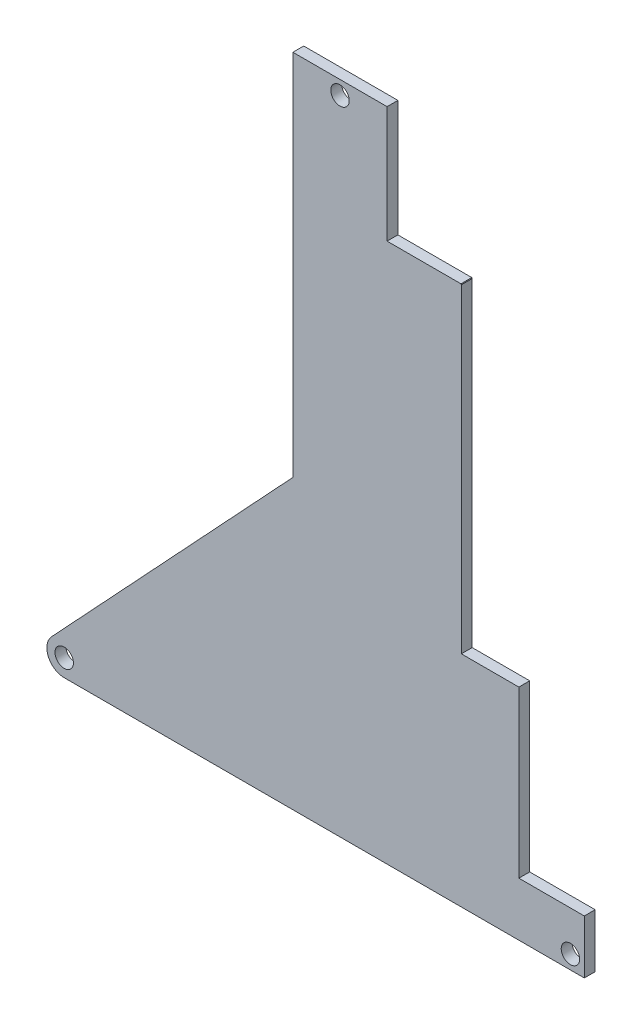
SolidWorks part; units mm, degrees
ref_plane "Front Plane" through (0, 0, 0) normal (0, 0, 1) x (1, 0, 0)
ref_plane "Top Plane" through (0, 0, 0) normal (0, 1, 0) x (1, 0, 0)
ref_plane "Right Plane" through (0, 0, 0) normal (1, 0, 0) x (0, 0, -1)
sketch "Sketch1" plane through (0, 0, 0) normal (0, 0, 1) x (1, 0, 0)
  line L1 (-52.6486, -67.2724) -> (-30.5784, -43.6209)
  line L3 (-30.5784, -43.6209) -> (-18.8373, -31.0385)
  line L4 (-18.8373, 22.9178) -> (-18.8373, 15.0967)
  line L5 (-62.4049, -73.074) -> (-22.4391, -30.2446) construction
  line L6 (-54.2124, -68.9483) -> (-52.6486, -67.2724)
  line L7 (-60.0836, -75.2401) -> (-20.1178, -32.4107) construction
  line L9 (23.8665, -73.2212) -> (-30.5784, -73.2212)
  line L12 (-18.8373, 15.0967) -> (-18.8373, -31.0385)
  line L13 (-30.5784, -73.2212) -> (-52.3554, -73.2212)
  line L14 (-18.8373, 22.9178) -> (-5.0365, 22.9178)
  line L20 (23.8665, -65.3472) -> (23.8665, -73.2212)
  arc A1 (25.454, -65.3472) -> (-3.6178, 23.6674) centre (-125.3585, -65.3472) ccw construction
  arc A2 (23.8665, -65.3472) -> (-5.0365, 22.9178) centre (-125.3585, -65.3472) ccw
  arc A3 (23.8665, -65.3472) -> (-4.8993, 22.7304) centre (-125.3585, -65.3472) ccw construction
  arc A7 (-52.3554, -73.2212) -> (-54.2124, -68.9483) centre (-52.3554, -70.6812) cw
  dimension "D5" = 2.54
  dimension "D1" = 1.5875
  dimension "D2" = 3.175
extrude "Boss-Extrude1" add sketch "Sketch1" along normal blind 1.5875
hole_wizard "#2 Clearance Hole1" positions "Sketch3" profile "Sketch2" hole size "#2" standard "ANSI Inch" end condition through all
sketch "Sketch3" plane through (0, 0, 0) normal (0, 0, -1) x (-1, 0, 0)
  line L0 (11.9369, 20.8858) -> (11.9369, 22.9178) construction
  line L1 (5.0365, 22.9178) -> (18.8373, 22.9178) construction
  line L2 (-23.8665, -73.2212) -> (-23.8665, -65.3472) construction
  line L3 (52.3554, -73.2212) -> (-23.8665, -73.2212) construction
  point P0 (-21.8345, -71.1892)
  point P2 (52.3554, -70.6812)
  point P5 (11.9369, 20.8858)
  dimension "D1" = 2.032
  dimension "D2" = 2.032
  dimension "D3" = 2.032
sketch "Sketch2" plane through (21.8345, -71.1892, 0) normal (1, 0, 0) x (0, 1, 0)
  line L0 (0, 0) -> (0, 1.5875)
  line L1 (0, 1.5875) -> (1.3525, 1.5875)
  line L2 (1.3525, 1.5875) -> (1.3525, 0)
  line L5 (1.3525, 0) -> (0, 0)
  line L11 (0, -6.35) -> (0, 107.95) construction
  dimension "Thru Hole Dia." = 2.7051
  dimension "Thru Hole Depth" = 1.5875
sketch "Sketch4" plane through (0, 0, 0) normal (0, 0, -1) x (-1, 0, 0)
  line L1 (-23.8665, -65.3472) -> (-14.278, -65.3472)
  line L2 (-23.8665, -65.3472) -> (-23.8665, -41.0902)
  line L3 (-23.8665, -41.0902) -> (-14.278, -41.0902)
  line L4 (-14.278, -65.3472) -> (-14.278, -41.0902)
  line L5 (-23.8665, -65.3472) -> (-14.278, -41.0902) construction
  line L6 (-23.8665, -41.0902) -> (-14.278, -65.3472) construction
  line L8 (-14.278, -41.0902) -> (-9.1472, -41.0902) construction
  line L9 (-14.278, -73.9832) -> (-14.278, -41.0902) construction
  line L10 (-5.8452, 5.8452) -> (-21.8817, 5.8452)
  line L11 (-5.8452, 5.8452) -> (-5.8452, -41.0902)
  line L12 (-5.8452, -41.0902) -> (-21.8817, -41.0902)
  line L13 (-21.8817, 5.8452) -> (-21.8817, -41.0902)
  line L14 (-5.8452, 5.8452) -> (-21.8817, -41.0902) construction
  line L15 (-5.8452, -41.0902) -> (-21.8817, 5.8452) construction
  line L16 (5.0365, 22.9178) -> (-5.8452, 22.9178)
  line L17 (5.0365, 22.9178) -> (5.0365, 5.8452)
  line L18 (5.0365, 5.8452) -> (-5.8452, 5.8452)
  line L19 (-5.8452, 22.9178) -> (-5.8452, 5.8452)
  line L20 (5.0365, 22.9178) -> (-5.8452, 5.8452) construction
  line L21 (5.0365, 5.8452) -> (-5.8452, 22.9178) construction
  arc A0 (5.0365, 22.9178) -> (-23.8665, -65.3472) centre (125.3585, -65.3472) ccw construction
  point P4 (-19.0722, -53.2187)
  point P14 (-13.8635, -17.6225)
  point P23 (-0.4043, 14.3815)
  arc M8 (5.0365, 22.9178) -> (-23.8665, -65.3472) centre (125.3585, -65.3472) ccw
extrude "Cut-Extrude1" cut sketch "Sketch4" against normal through all contours L1 L4 L3 M8 | L12 L11 L3 M8 | L18 L17 M8
